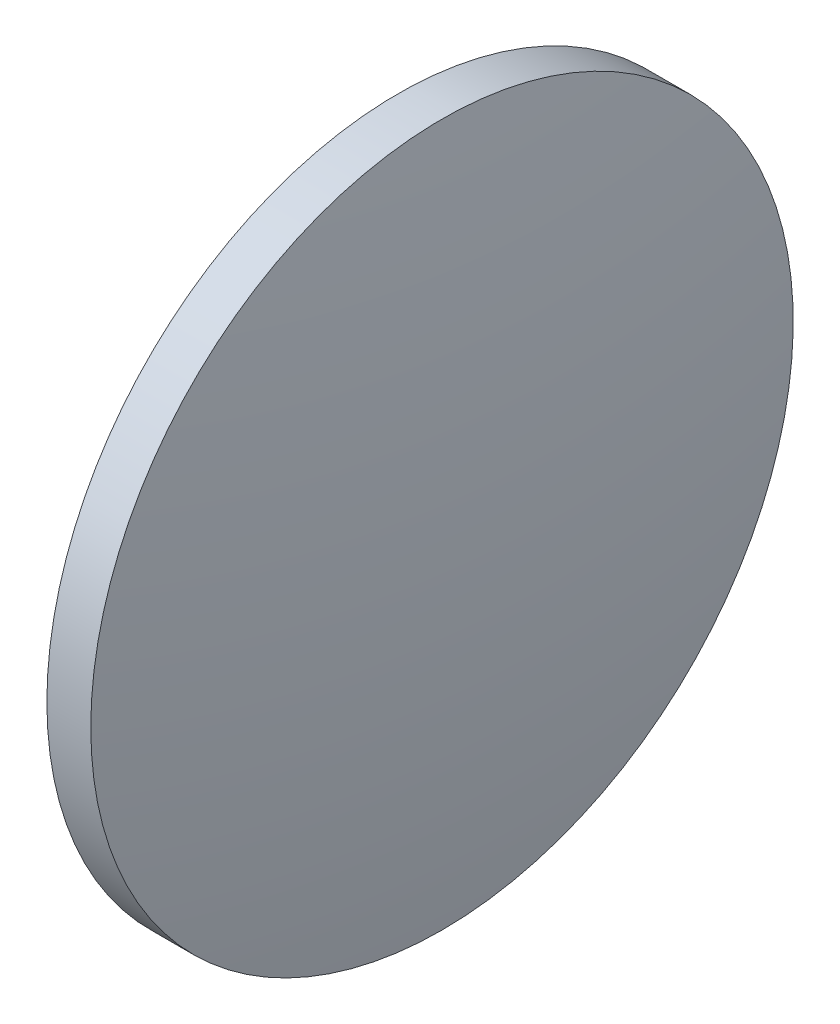
SolidWorks part; units mm, degrees
ref_plane "前视基准面" through (0, 0, 0) normal (0, 0, 1) x (1, 0, 0)
ref_plane "上视基准面" through (0, 0, 0) normal (0, 1, 0) x (1, 0, 0)
ref_plane "右视基准面" through (0, 0, 0) normal (1, 0, 0) x (0, 0, -1)
sketch "草图1" plane through (0, 0, 0) normal (0, 0, 1) x (1, 0, 0)
  line L0 (445.2534, 48.34) -> (464.4296, 48.34) construction
  line L1 (449.948, 48.34) -> (449.948, 68.34)
  line L2 (454.008, 48.34) -> (449.948, 48.34)
  line L5 (449.948, 68.34) -> (452.448, 68.34)
  arc A0 (454.008, 48.34) -> (452.448, 68.34) centre (325.0228, 48.34) ccw
revolve "旋转1" add sketch "草图1" angle 360 about L0
